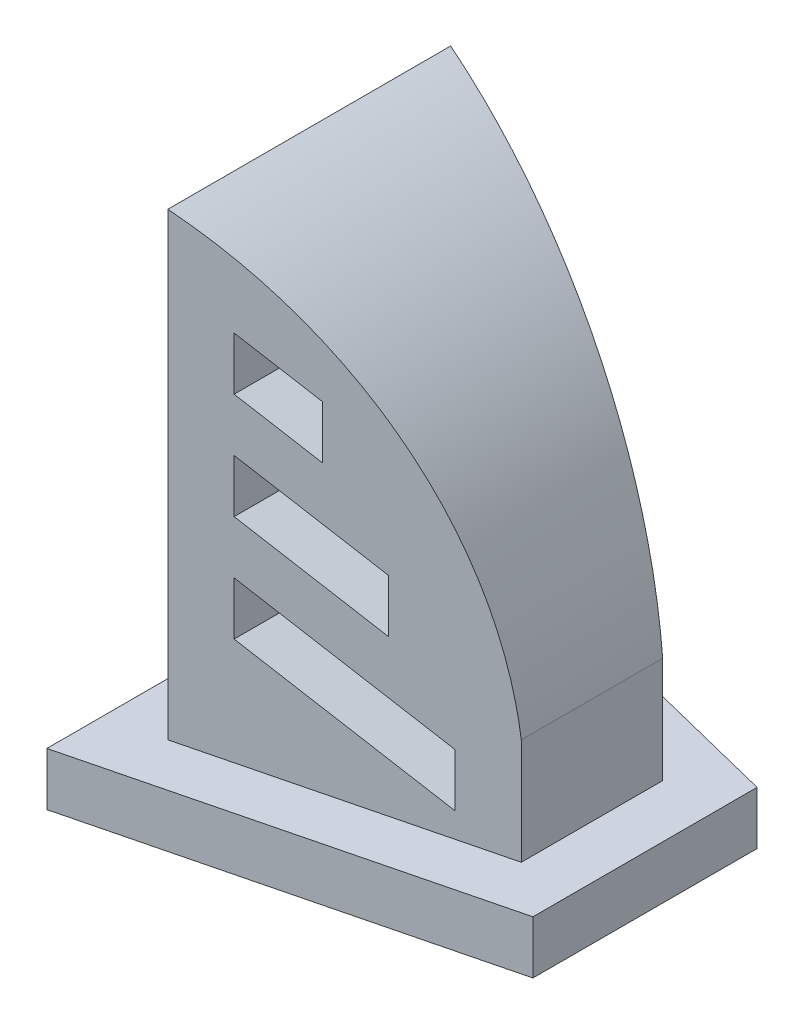
SolidWorks part; units mm, degrees
other "Perspective"
ref_plane "Front Plane" through (0, 0, 0) normal (0, 0, 1) x (1, 0, 0)
ref_plane "Top Plane" through (0, 0, 0) normal (0, 1, 0) x (1, 0, 0)
ref_plane "Right Plane" through (0, 0, 0) normal (1, 0, 0) x (0, 0, -1)
sketch "Sketch1" plane through (0, 0, 0) normal (0, 1, 0) x (1, 0, 0)
  line L0 (0, 0) -> (-80, -20) construction
  line L1 (-80, -20) -> (-80, 60) construction
  line L2 (-80, 60) -> (0, 40) construction
  line L3 (0, 40) -> (0, 0) construction
  line L4 (0, 20) -> (-80, 20) construction
  line L5 (15, -11.7116) -> (-95, -39.2116)
  line L6 (-95, 79.2116) -> (15, 51.7116)
  line L7 (15, 51.7116) -> (15, -11.7116)
  line L8 (-95, -39.2116) -> (-95, 79.2116)
  line L9 (15, 40) -> (15, 0) construction
  line L10 (-76.362, 74.5521) -> (3.638, 54.5521) construction
  line L11 (3.638, -14.5521) -> (-76.362, -34.5521) construction
  line L12 (-95, -20) -> (-95, 60) construction
  dimension "D1" = 40
  dimension "D2" = 80
  dimension "D3" = 80
  dimension "D4" = 15
  dimension "D5" = 15
  dimension "D6" = 15
  dimension "D7" = 15
extrude "Extrude1" add sketch "Sketch1" along normal blind 15
sketch "Sketch2" plane through (0, 15, 0) normal (0, 1, 0) x (1, 0, 0)
  line L0 (0, 0) -> (0, 40)
  line L1 (0, 40) -> (-80, 60)
  line L2 (-80, 60) -> (-80, -20)
  line L3 (-80, -20) -> (0, 0)
extrude "Extrude2" add sketch "Sketch2" along normal blind 130
sketch "Sketch3" plane through (0, 0, 0) normal (0, 0, 1) x (1, 0, 0)
  line L0 (-80, 145) -> (0, 145)
  line L1 (0, 145) -> (0, 45)
  line L3 (-65, 120.31) -> (-65, 105.31)
  line L4 (-65, 45.31) -> (-15, 21.9946)
  line L5 (-65, 60.31) -> (-15, 36.9946)
  line L6 (-15, 36.9946) -> (-15, 21.9946)
  line L7 (-65, 75.31) -> (-30, 58.9892)
  line L8 (-30, 58.9892) -> (-30, 73.9892)
  line L9 (-30, 73.9892) -> (-65, 90.31)
  line L10 (-65, 105.31) -> (-45, 95.9838)
  line L11 (-45, 95.9838) -> (-45, 110.9838)
  line L12 (-45, 110.9838) -> (-65, 120.31)
  line L13 (-65, 90.31) -> (-65, 75.31)
  line L14 (-65, 60.31) -> (-65, 45.31)
  line L15 (-95, 15) -> (15, 15) construction
  line L16 (-15, 21.9946) -> (0, 15) construction
  line L17 (-80, 145) -> (-80, 15) construction
  arc A0 (0, 45) -> (-80, 145) centre (-119.2495, 31.6004) ccw
  dimension "D1" = 120
  dimension "D2" = 25
  dimension "D3" = 15
  dimension "D4" = 15
  dimension "D5" = 15
  dimension "D6" = 15
  dimension "D7" = 15
  dimension "D8" = 30
  dimension "D9" = 15
  dimension "D10" = 20
  dimension "D11" = 15
  dimension "D12" = 15
extrude "Extrude3" cut sketch "Sketch3" against normal mid plane 130
